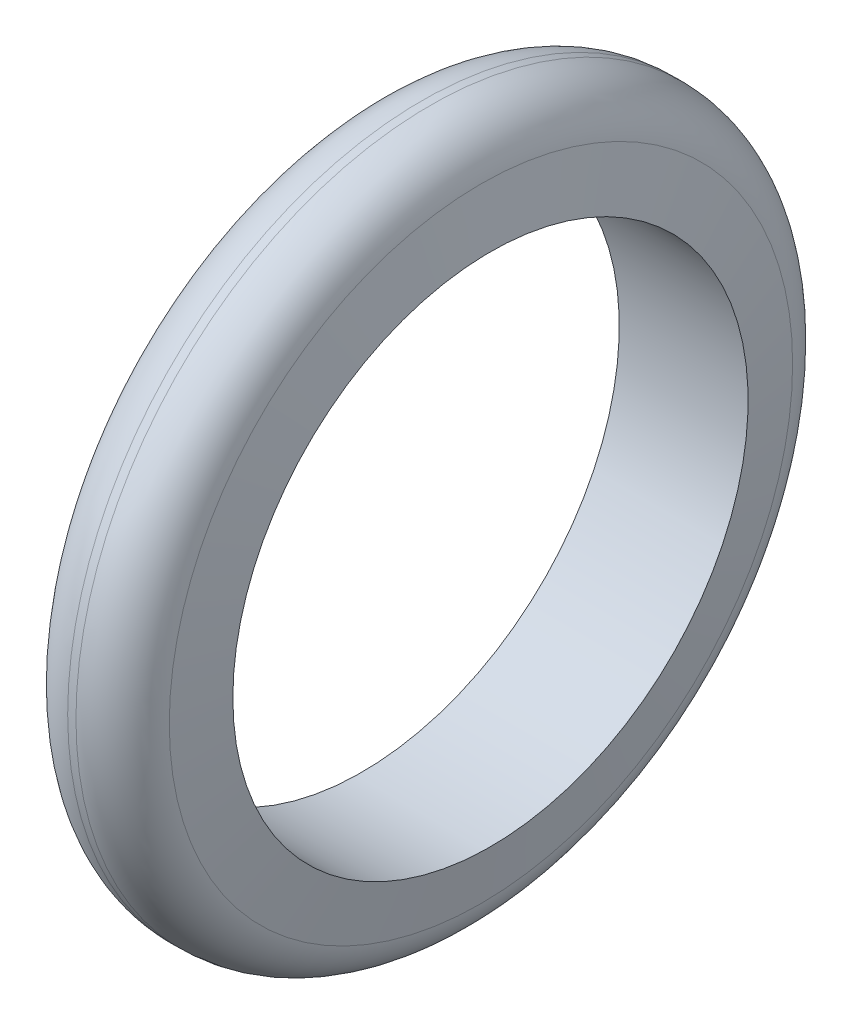
SolidWorks part; units mm, degrees
ref_plane "Front Plane" through (0, 0, 0) normal (0, 0, 1) x (1, 0, 0)
ref_plane "Top Plane" through (0, 0, 0) normal (0, 1, 0) x (1, 0, 0)
ref_plane "Right Plane" through (0, 0, 0) normal (1, 0, 0) x (0, 0, -1)
sketch "Sketch1" plane through (0, 0, 0) normal (0, 1, 0) x (1, 0, 0)
  line L0 (0, 0) -> (0, 82.4425) construction
  line L1 (0, 0) -> (94.567, 0) construction
  line L2 (-10, 40) -> (10, 40)
  line L3 (10, 40) -> (7.3551, 55)
  line L4 (7.3551, 55) -> (-7.3551, 55)
  line L5 (-7.3551, 55) -> (-10, 40)
  dimension "D1" = 10
  dimension "D2" = 80
  dimension "D3" = 110
  dimension "D4" = 20
revolve "Revolve1" add sketch "Sketch1" angle 360 about L1
fillet "Fillet1" radius 8 2 edges at (-7.3551, 0, 55) (7.3551, 0, 55)
